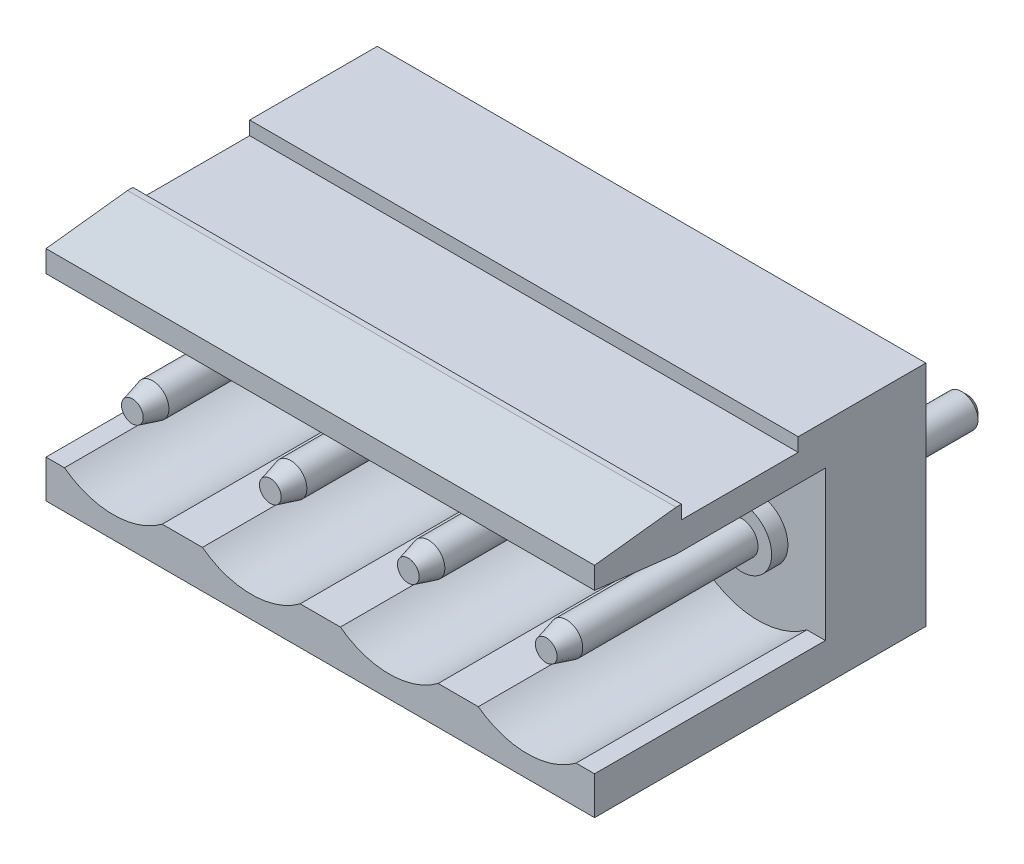
SolidWorks part; units mm, degrees
ref_plane "Plan de face" through (0, 0, 0) normal (0, 0, 1) x (1, 0, 0)
ref_plane "Plan de dessus" through (0, 0, 0) normal (0, 1, 0) x (1, 0, 0)
ref_plane "Plan de droite" through (0, 0, 0) normal (1, 0, 0) x (0, 0, -1)
sketch "Esquisse1" plane through (0, 0, 0) normal (0, 0, 1) x (1, 0, 0)
  line L1 (0, 0) -> (20.2, 0)
  line L2 (0, 0) -> (0, 8.4)
  line L3 (0, 8.4) -> (20.2, 8.4)
  line L4 (20.2, 0) -> (20.2, 8.4)
  dimension "D1" = 20.2
  dimension "D2" = 8.4
extrude "Boss.-Extru.1" add sketch "Esquisse1" along normal blind 12.2
sketch "Esquisse2" plane through (0, 0, 12.2) normal (0, 0, 1) x (1, 0, 0)
  line L0 (0, 8.4) -> (0, 0) construction
  line L2 (0, 1.4) -> (0, 6.9)
  line L3 (0, 6.9) -> (20.2, 6.9)
  line L4 (20.2, 1.4) -> (20.2, 6.9)
  line L5 (20.2, 0) -> (20.2, 8.4) construction
  line L7 (4.28, 1.4) -> (5.76, 1.4)
  line L9 (2.48, 3.8) -> (7.56, 3.8) construction
  line L10 (0, 0) -> (20.2, 0) construction
  line L11 (20.2, 8.4) -> (0, 8.4) construction
  line L12 (9.36, 1.4) -> (10.84, 1.4)
  line L13 (14.44, 1.4) -> (15.92, 1.4)
  line L14 (19.52, 1.4) -> (20.2, 1.4)
  line L15 (0, 1.4) -> (0.68, 1.4)
  line L16 (7.56, 3.8) -> (12.64, 3.8) construction
  line L17 (12.64, 3.8) -> (17.72, 3.8) construction
  arc A0 (0.68, 1.4) -> (4.28, 1.4) centre (2.48, 3.8) ccw
  arc A1 (5.76, 1.4) -> (9.36, 1.4) centre (7.56, 3.8) ccw
  arc A2 (10.84, 1.4) -> (14.44, 1.4) centre (12.64, 3.8) ccw
  arc A3 (15.92, 1.4) -> (19.52, 1.4) centre (17.72, 3.8) ccw
  point P24 (0.8659, 1.4)
  dimension "D2" = 3
  dimension "D1" = 5.08
  dimension "D3" = 3.8
  dimension "D4" = 1.4
  dimension "D5" = 1.5
extrude "Enlèv. mat.-Extru.1" cut sketch "Esquisse2" against normal blind 8.5
sketch "Esquisse3" plane through (0, 0, 0) normal (-1, 0, 0) x (0, 0, 1)
  line L0 (12.2, 8.4) -> (0, 8.4) construction
  line L1 (4.7, 8.4) -> (9, 8.4)
  line L2 (4.7, 8.4) -> (4.7, 7.9)
  line L3 (4.7, 7.9) -> (9, 7.9)
  line L4 (9, 8.4) -> (9, 7.9)
  line L5 (12.2, 8.4) -> (12.2, 6.9) construction
  line L6 (12.2, 8.4) -> (9.2, 8.4)
  line L7 (9.2, 8.4) -> (12.2, 8.05)
  line L8 (12.2, 8.05) -> (12.2, 8.4)
  line L9 (12.2, 7.25) -> (12.2, 6.9)
  line L10 (12.2, 6.9) -> (9.2, 6.9)
  line L11 (3.7, 6.9) -> (12.2, 6.9) construction
  line L12 (9.2, 6.9) -> (12.2, 7.25)
  point P15 (0, 0)
  dimension "D1" = 0.5
  dimension "D2" = 4.3
  dimension "D3" = 3.2
  dimension "D4" = 3
  dimension "D5" = 0.8
extrude "Enlèv. mat.-Extru.2" cut sketch "Esquisse3" against normal through all
sketch "Esquisse4" plane through (0, 0, 0) normal (0, 0, -1) x (-1, 0, 0)
  line L0 (-20.2, 3.75) -> (-17.72, 3.75) construction
  line L1 (-20.2, 0) -> (-20.2, 8.4) construction
  line L2 (-17.72, 3.75) -> (-12.64, 3.75) construction
  line L3 (-12.64, 3.75) -> (-7.56, 3.75) construction
  line L5 (0, 0) -> (-20.2, 0) construction
  line L7 (-7.56, 3.75) -> (-2.48, 3.75) construction
  line L8 (-2.48, 3.75) -> (0, 3.75) construction
  line L9 (0, 6.9) -> (0, 1.4) construction
  circle A0 centre (-17.72, 3.75) radius 0.6
  circle A1 centre (-12.64, 3.75) radius 0.6
  circle A2 centre (-2.48, 3.75) radius 0.6
  circle A3 centre (-7.56, 3.75) radius 0.6
  dimension "D2" = 1.2
  dimension "D1" = 5.08
  dimension "D3" = 3.75
extrude "Boss.-Extru.2" add sketch "Esquisse4" along normal blind 4 and the other way blind 11.5
chamfer "Chanfrein1" distance 0.2 angle 75 4 edges at (17.12, 3.75, 11.5) (12.04, 3.75, 11.5) (1.88, 3.75, 11.5) (6.96, 3.75, 11.5)
chamfer "Chanfrein2" distance 0.2 angle 45 4 edges at (17.12, 3.75, -4) (12.04, 3.75, -4) (1.88, 3.75, -4) (6.96, 3.75, -4)
sketch "Esquisse5" plane through (0, 0, 3.7) normal (0, 0, 1) x (1, 0, 0)
  circle A0 centre (12.64, 3.75) radius 1.1
  circle A1 centre (17.72, 3.75) radius 1.1
  circle A2 centre (7.56, 3.75) radius 1.1
  circle A3 centre (2.48, 3.75) radius 1.1
  dimension "D1" = 2.2
extrude "Boss.-Extru.3" add sketch "Esquisse5" along normal blind 0.6
